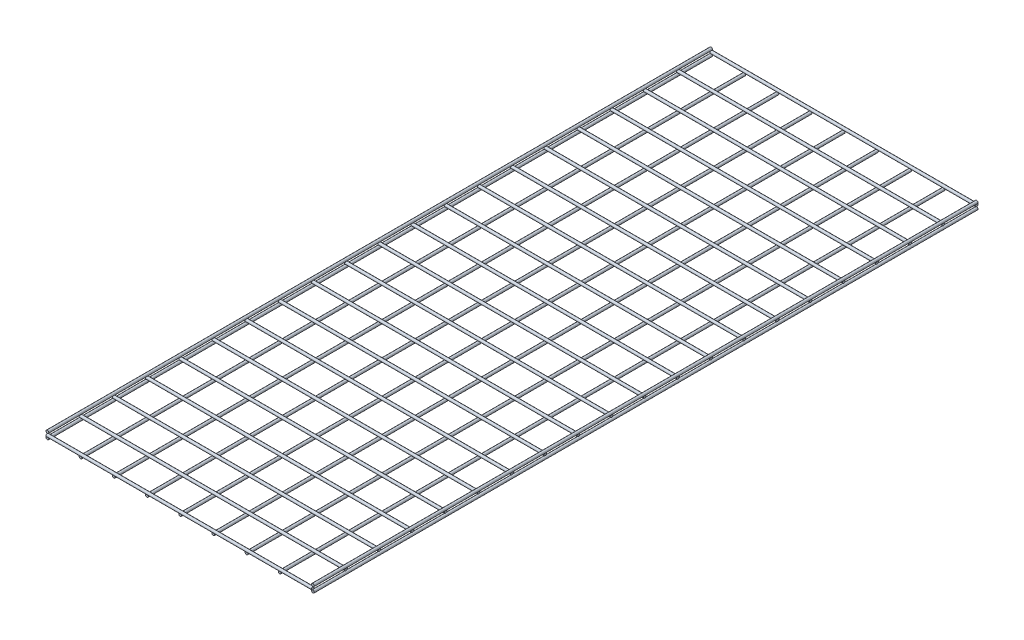
SolidWorks part; units mm, degrees
material "Plain Carbon Steel"
ref_plane "Front Plane" through (0, 0, 0) normal (0, 0, 1) x (1, 0, 0)
ref_plane "Top Plane" through (0, 0, 0) normal (0, 1, 0) x (1, 0, 0)
ref_plane "Right Plane" through (0, 0, 0) normal (1, 0, 0) x (0, 0, -1)
sketch "Sketch1" plane through (0, 0, 0) normal (0, 0, 1) x (1, 0, 0)
  line L0 (0, -55) -> (0, 55) construction
  circle A0 centre (0, 0) radius 3.175
  circle A1 centre (0, 12.7) radius 3.175
  circle A2 centre (76.2, 0) radius 3.175
  circle A3 centre (152.4, 0) radius 3.175
  circle A4 centre (228.6, 0) radius 3.175
  circle A5 centre (304.8, 0) radius 3.175
  circle A6 centre (381, 0) radius 3.175
  circle A7 centre (457.2, 0) radius 3.175
  circle A8 centre (533.4, 0) radius 3.175
  circle A9 centre (609.6, 0) radius 3.175
  circle A10 centre (609.6, 12.7) radius 3.175
  dimension "D1" = 6.35
  dimension "D2" = 6.35
  dimension "D6" = 6.35
  dimension "D3" = 12.7
  dimension "D5" = 12.7
  dimension "D4" = 9
extrude "Boss-Extrude1" add sketch "Sketch1" along normal blind 1524
sketch "Sketch2" plane through (0, 0, 0) normal (1, 0, 0) x (0, 0, -1)
  line L0 (0, 15.875) -> (-1524, 15.875) construction
  line L1 (0, 10.4775) -> (0, -10.4775) construction
  circle A0 centre (0, 6.35) radius 3.175
  circle A1 centre (-76.2, 6.35) radius 3.175
  circle A2 centre (-152.4, 6.35) radius 3.175
  circle A3 centre (-228.6, 6.35) radius 3.175
  circle A4 centre (-304.8, 6.35) radius 3.175
  circle A5 centre (-381, 6.35) radius 3.175
  circle A6 centre (-457.2, 6.35) radius 3.175
  circle A7 centre (-533.4, 6.35) radius 3.175
  circle A8 centre (-609.6, 6.35) radius 3.175
  circle A9 centre (-685.8, 6.35) radius 3.175
  circle A10 centre (-762, 6.35) radius 3.175
  circle A11 centre (-838.2, 6.35) radius 3.175
  circle A12 centre (-914.4, 6.35) radius 3.175
  circle A13 centre (-990.6, 6.35) radius 3.175
  circle A14 centre (-1066.8, 6.35) radius 3.175
  circle A15 centre (-1143, 6.35) radius 3.175
  circle A16 centre (-1219.2, 6.35) radius 3.175
  circle A17 centre (-1295.4, 6.35) radius 3.175
  circle A18 centre (-1371.6, 6.35) radius 3.175
  circle A19 centre (-1447.8, 6.35) radius 3.175
  circle A20 centre (-1524, 6.35) radius 3.175
  dimension "D2" = 6.35
  dimension "D1" = 9.525
  dimension "D3" = 0
  dimension "D4" = 21
extrude "Boss-Extrude2" add sketch "Sketch2" along normal blind 609.6 separate body
ref_plane "Plane1" through (304.8, 0, 0) normal (1, 0, 0) x (0, 0, -1)
ref_plane "Plane2" through (0, 0, 762) normal (0, 0, 1) x (1, 0, 0)
